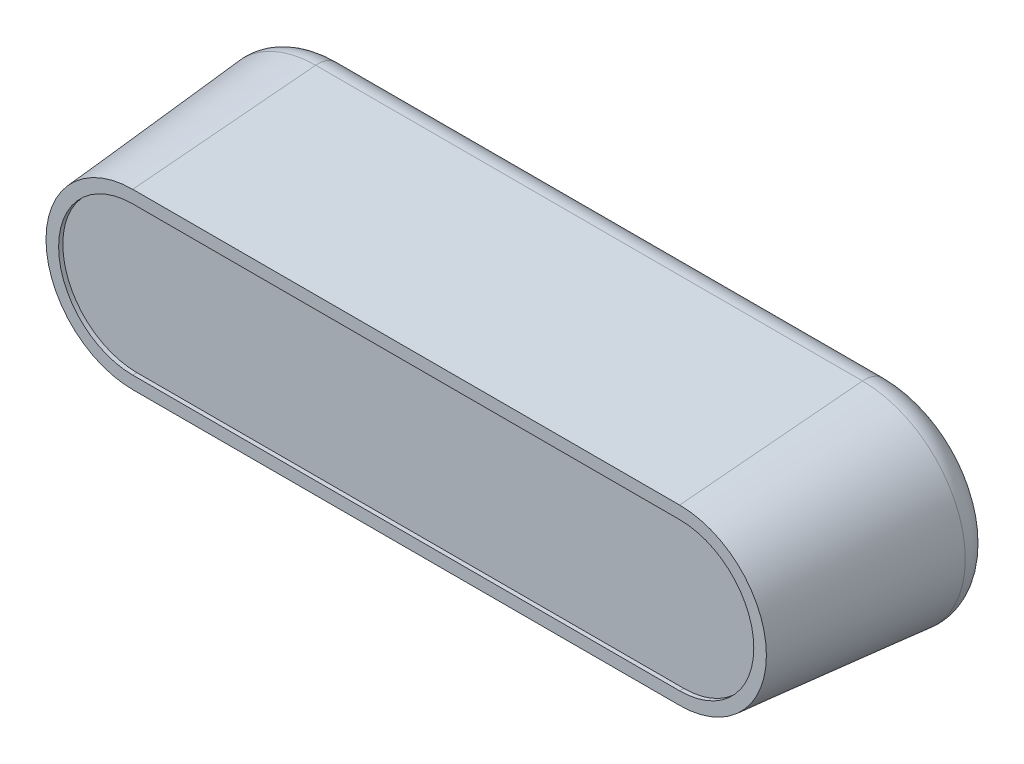
SolidWorks part; units mm, degrees
ref_plane "Front Plane" through (0, 0, 0) normal (0, 0, 1) x (1, 0, 0)
ref_plane "Top Plane" through (0, 0, 0) normal (0, 1, 0) x (1, 0, 0)
ref_plane "Right Plane" through (0, 0, 0) normal (1, 0, 0) x (0, 0, -1)
sketch "Sketch1" plane through (0, 0, 0) normal (0, 0, 1) x (1, 0, 0)
  line L0 (-32.5, 0) -> (32.5, 0) construction
  line L1 (-32.5, 12.5) -> (32.5, 12.5)
  line L2 (-32.5, -12.5) -> (32.5, -12.5)
  arc A0 (-32.5, 12.5) -> (-32.5, -12.5) centre (-32.5, 0) ccw
  arc A1 (32.5, -12.5) -> (32.5, 12.5) centre (32.5, 0) ccw
  point P2 (0, 0)
  dimension "D1" = 12.5
  dimension "D2" = 65
extrude "Boss-Extrude1" add sketch "Sketch1" along normal blind 25 draft 5
fillet "Fillet1" radius 3 4 edges at (0, -12.5, 0) (45, 0, 0) (0, 12.5, 0) (-45, 0, 0)
sketch "Sketch4" plane through (0, 0, 25) normal (0, 0, 1) x (1, 0, 0)
  line L0 (32.5, 8.8128) -> (-32.5, 8.8128)
  line L1 (-32.5, -8.8128) -> (32.5, -8.8128)
  line L2 (-32.5, -10.3128) -> (32.5, -10.3128)
  line L3 (32.5, 10.3128) -> (-32.5, 10.3128)
  line L4 (-32.5, -10.3128) -> (32.5, -10.3128)
  line L5 (32.5, 10.3128) -> (-32.5, 10.3128)
  arc A0 (-32.5, 8.8128) -> (-32.5, -8.8128) centre (-32.5, 0) ccw
  arc A1 (32.5, -8.8128) -> (32.5, 8.8128) centre (32.5, 0) ccw
  arc A2 (-32.5, 10.3128) -> (-32.5, -10.3128) centre (-32.5, 0) ccw
  arc A3 (32.5, -10.3128) -> (32.5, 10.3128) centre (32.5, 0) ccw
  arc A4 (-32.5, 10.3128) -> (-32.5, -10.3128) centre (-32.5, 0) ccw
  arc A5 (32.5, -10.3128) -> (32.5, 10.3128) centre (32.5, 0) ccw
  dimension "D1" = 0
  dimension "D2" = 1.5
extrude "Cut-Extrude1" cut sketch "Sketch4" against normal blind 0.5 contours L1 A1 L0 A0
ref_plane "Plane3" through (0, -12.5, 0) normal (0, 1, 0) x (1, 0, 0)
sketch "Sketch5" plane through (0, -12.5, 0) normal (0, 1, 0) x (1, 0, 0)
  line L0 (-32.5, -25) -> (-32.5, -3.2615) construction
  line L1 (32.5, -3.2615) -> (-32.5, -3.2615)
  line L2 (32.5, -3.2615) -> (32.5, -12.2615)
  line L3 (32.5, -12.2615) -> (-32.5, -12.2615)
  line L4 (-32.5, -3.2615) -> (-32.5, -12.2615)
  dimension "D1" = 9
extrude "Boss-Extrude2" add sketch "Sketch5" along normal up to next
sketch "Sketch6" plane through (0, -12.5, 0) normal (0, -1, 0) x (1, 0, 0)
  circle A0 centre (0, 8) radius 2.5
  dimension "D1" = 5
  dimension "D2" = 8
extrude "Cut-Extrude2" cut sketch "Sketch6" against normal blind 8
